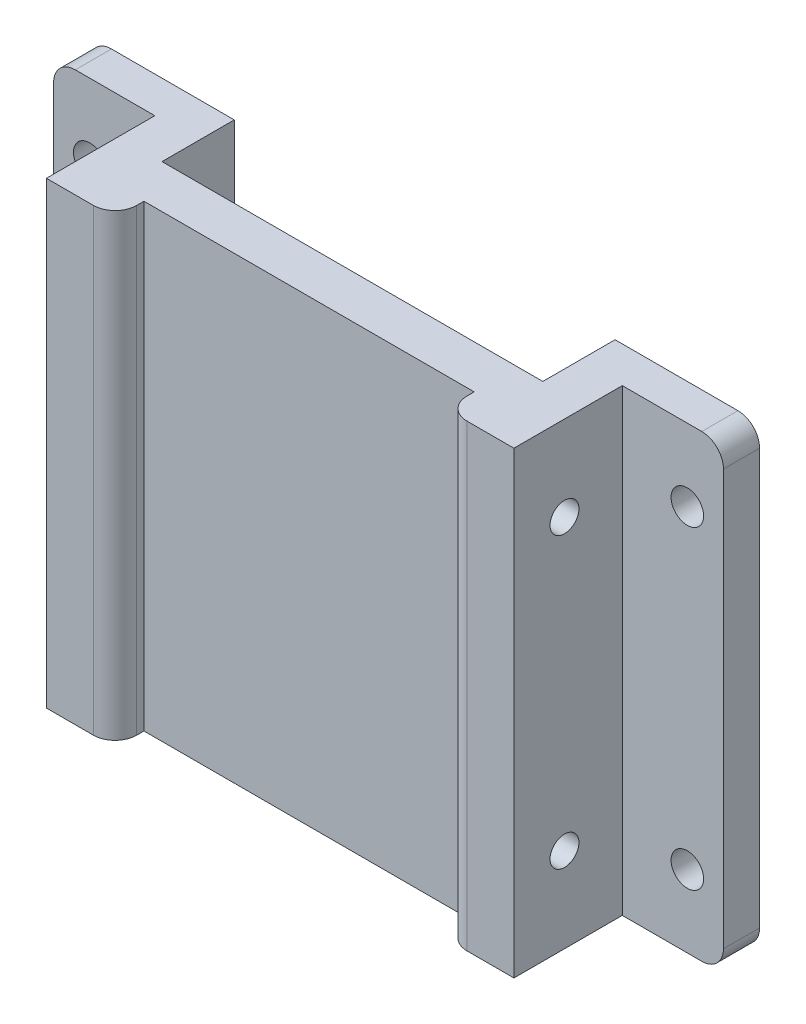
SolidWorks part; units mm, degrees
ref_plane "Front Plane" through (0, 0, 0) normal (0, 0, 1) x (1, 0, 0)
ref_plane "Top Plane" through (0, 0, 0) normal (0, 1, 0) x (1, 0, 0)
ref_plane "Right Plane" through (0, 0, 0) normal (1, 0, 0) x (0, 0, -1)
sketch "Sketch1" plane through (0, 0, 0) normal (0, 0, 1) x (1, 0, 0)
  line L0 (0, 0) -> (0, 108.2433) construction
  line L1 (-46.35, 31.75) -> (-26.35, 31.75)
  line L2 (-46.35, 31.75) -> (-46.35, -31.75)
  line L3 (-46.35, -31.75) -> (-26.35, -31.75)
  line L4 (-26.35, 31.75) -> (-26.35, -31.75)
  line L5 (26.35, 31.75) -> (26.35, -31.75)
  line L6 (46.35, -31.75) -> (26.35, -31.75)
  line L7 (46.35, 31.75) -> (46.35, -31.75)
  line L8 (46.35, 31.75) -> (26.35, 31.75)
  line L9 (-35.35, 31.75) -> (-32.35, 31.75) construction
  line L10 (-35.35, -31.75) -> (-32.35, -31.75) construction
  line L11 (-46.35, 35.25) -> (-46.35, -24.3581) construction
  point P9 (-33.85, 31.75)
  dimension "D1" = 20
extrude "Boss-Extrude1" add sketch "Sketch1" along normal blind 5
sketch "Sketch2" plane through (0, 0, 5) normal (0, 0, 1) x (1, 0, 0)
  line L0 (-46.35, -31.75) -> (-26.35, -31.75) construction
  line L1 (-26.35, 31.75) -> (-32.35, 31.75)
  line L2 (-26.35, 31.75) -> (-26.35, -31.75)
  line L3 (-26.35, -31.75) -> (-32.35, -31.75)
  line L4 (-32.35, 31.75) -> (-32.35, -31.75)
  line L5 (0, 0) -> (0, 72.5) construction
  line L6 (21.5, 72.5) -> (-21.5, 72.5) construction
  line L7 (32.35, 31.75) -> (32.35, -31.75)
  line L8 (26.35, -31.75) -> (32.35, -31.75)
  line L9 (26.35, 31.75) -> (26.35, -31.75)
  line L10 (26.35, 31.75) -> (32.35, 31.75)
  dimension "D1" = 6
extrude "Boss-Extrude2" add sketch "Sketch2" along normal blind 15
sketch "Sketch3" plane through (-26.35, 0, 0) normal (1, 0, 0) x (0, 0, -1)
  line L0 (-20, 31.75) -> (0, 31.75) construction
  line L1 (-16, -31.75) -> (-10, -31.75)
  line L2 (-16, -31.75) -> (-16, 31.75)
  line L3 (-16, 31.75) -> (-10, 31.75)
  line L4 (-10, -31.75) -> (-10, 31.75)
  line L5 (-20, -31.75) -> (0, -31.75) construction
  line L6 (-20, -31.75) -> (-20, 31.75) construction
  dimension "D1" = 4
  dimension "D2" = 6
extrude "Boss-Extrude3" add sketch "Sketch3" along normal up to next
sketch "Sketch4" plane through (-26.35, 0, 0) normal (1, 0, 0) x (0, 0, -1)
  line L1 (-20, 31.75) -> (-16, 31.75)
  line L2 (-20, 31.75) -> (-20, -31.75)
  line L3 (-20, -31.75) -> (-16, -31.75)
  line L4 (-16, 31.75) -> (-16, -31.75)
extrude "Boss-Extrude4" add sketch "Sketch4" along normal blind 3.5
mirror "Mirror1" about plane through (0, 0, 0) normal (1, 0, 0) of "Boss-Extrude4"
sketch "Sketch6" plane through (0, 0, 5) normal (0, 0, 1) x (1, 0, 0)
  line L0 (-41.35, 31.75) -> (-41.35, -27.8581) construction
  line L1 (-32.35, 31.75) -> (-46.35, 31.75) construction
  line L2 (-46.35, -31.75) -> (-32.35, -31.75) construction
  line L3 (0, 31.75) -> (0, -31.75) construction
  line L4 (22.85, 31.75) -> (-22.85, 31.75) construction
  line L5 (22.85, -31.75) -> (-22.85, -31.75) construction
  line L6 (41.35, 31.75) -> (41.35, -27.8581) construction
  line L7 (-46.35, 31.75) -> (-46.35, -31.75) construction
  circle A0 centre (-41.35, 21.75) radius 2.25
  circle A1 centre (-41.35, -21.75) radius 2.25
  circle A2 centre (41.35, -21.75) radius 2.25
  circle A3 centre (41.35, 21.75) radius 2.25
  dimension "D1" = 4.5
  dimension "D4" = 4.5
  dimension "D2" = 10
  dimension "D3" = 10
  dimension "D5" = 5
extrude "Cut-Extrude2" cut sketch "Sketch6" against normal through all contours A0 | A1 | A2 | A3
fillet "Fillet1" radius 3 6 edges at (46.35, -31.75, 2.5) (46.35, 31.75, 2.5) (-46.35, -31.75, 2.5) (-46.35, 31.75, 2.5) (-22.85, 0, 20) (22.85, 0, 20)
sketch "Sketch7" plane through (-32.35, 0, 0) normal (-1, 0, 0) x (0, 0, 1)
  circle A0 centre (13, 20) radius 2
  circle A1 centre (13, -20) radius 2
  dimension "D1" = 4
  dimension "D2" = 4
extrude "Cut-Extrude6" cut sketch "Sketch7" against normal blind 15 contours A0 | A1
mirror "Mirror2" about plane through (0, 0, 0) normal (1, 0, 0) of "Cut-Extrude6"
